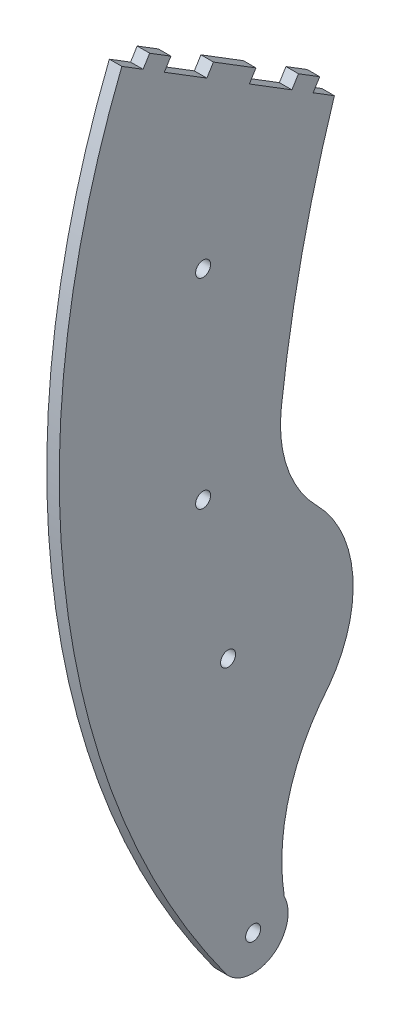
SolidWorks part; units mm, degrees
ref_plane "Alzado" through (0, 0, 0) normal (0, 0, 1) x (1, 0, 0)
ref_plane "Planta" through (0, 0, 0) normal (0, 1, 0) x (1, 0, 0)
ref_plane "Vista lateral" through (0, 0, 0) normal (1, 0, 0) x (0, 0, -1)
sketch "Croquis1" plane through (0, 0, 0) normal (1, 0, 0) x (0, 0, -1)
  line L0 (0, 0) -> (0, -50) construction
  line L1 (0, 0) -> (0, 100) construction
  line L2 (0, -50) -> (5, -50) construction
  line L3 (5, -50) -> (0, 0) construction
  line L4 (-5, 70) -> (-5, -93.0772) construction
  line L5 (21.2519, 86.8335) -> (-21.2519, 113.1665) construction
  line L6 (21.2519, 86.8335) -> (17.0015, 89.4668)
  line L7 (17.0015, 89.4668) -> (18.3182, 91.592)
  line L8 (-15.6849, 112.6584) -> (-11.4345, 110.0251)
  line L9 (-15.6849, 112.6584) -> (-17.0015, 110.5332)
  line L10 (-17.0015, 110.5332) -> (-21.2519, 113.1665)
  line L11 (-11.4345, 110.0251) -> (-12.7512, 107.8999)
  line L12 (-12.7512, 107.8999) -> (-4.2504, 102.6333)
  line L13 (-4.2504, 102.6333) -> (-2.9337, 104.7585)
  line L14 (-2.9337, 104.7585) -> (5.567, 99.4919)
  line L15 (5.567, 99.4919) -> (4.2504, 97.3667)
  line L16 (4.2504, 97.3667) -> (12.7512, 92.1001)
  line L17 (12.7512, 92.1001) -> (14.0678, 94.2253)
  line L18 (14.0678, 94.2253) -> (18.3182, 91.592)
  circle A0 centre (5, -50) radius 1.5
  arc A1 (-0.3708, -54.4894) -> (11.2267, -46.8019) centre (5, -50) ccw
  circle A2 centre (0, 100) radius 25 construction
  arc A3 (21.2519, 86.8335) -> (10.6459, 38.206) centre (268.8107, 7.3687) ccw
  arc A4 (-21.2519, 113.1665) -> (-0.3708, -54.4894) centre (140.988, 48.2448) ccw
  circle A5 centre (0, 100) radius 1.5 construction
  circle A6 centre (0, 0) radius 1.5
  circle A7 centre (0, 0) radius 25 construction
  circle A8 centre (-5, 30) radius 1.5
  circle A9 centre (-5, 70) radius 1.5
  arc A10 (20.2211, -14.7006) -> (11.2267, -46.8019) centre (50.7369, -40.5614) ccw
  arc A11 (10.6459, 38.206) -> (17.7347, 17.6204) centre (35.4694, 35.2409) ccw
  arc A12 (20.2211, -14.7006) -> (17.7347, 17.6204) centre (0, 0) ccw
  point P26 (9.2936, 23.2084)
  dimension "D1" = 3
  dimension "D2" = 50
  dimension "D3" = 5
  dimension "D4" = 100
  dimension "D5" = 25
  dimension "D11" = 25
  dimension "D6" = 40
  dimension "D7" = 5
  dimension "D8" = 30
  dimension "D9" = 25
  dimension "D10" = 7
  dimension "D13" = 40
extrude "Saliente-Extruir1" add sketch "Croquis1" along normal blind 2.5
